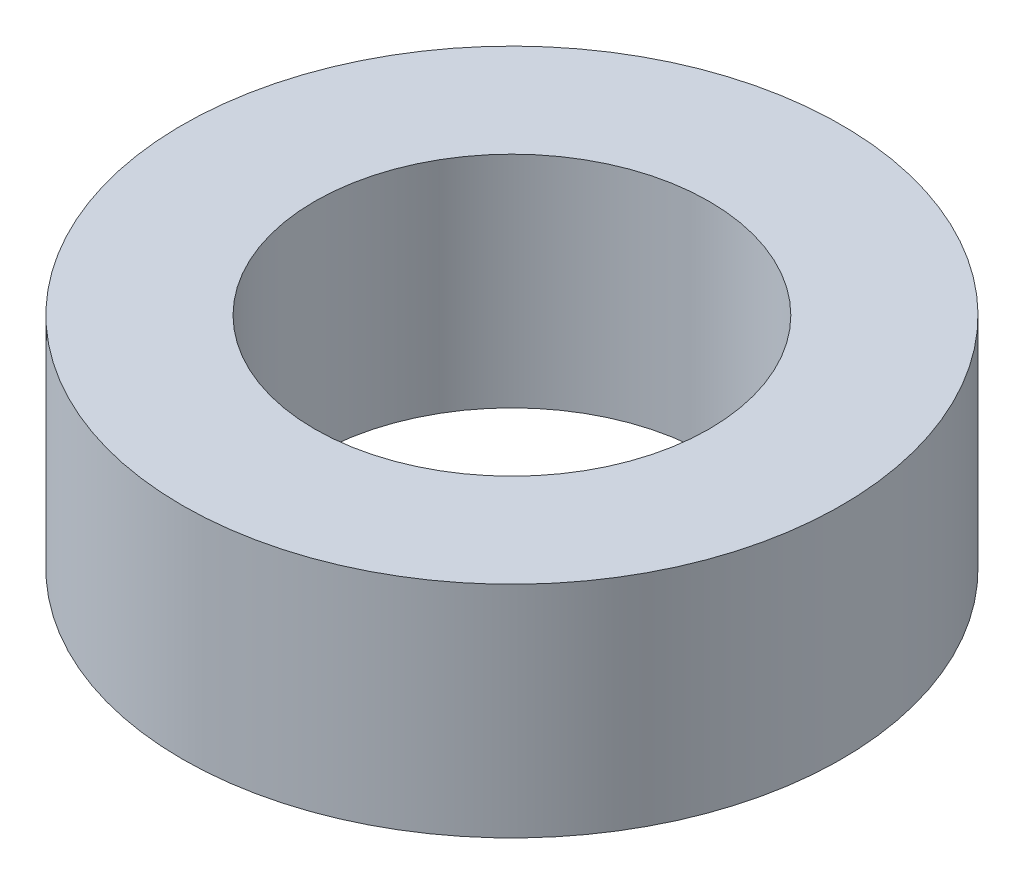
SolidWorks part; units mm, degrees
ref_plane "Front Plane" through (0, 0, 0) normal (0, 0, 1) x (1, 0, 0)
ref_plane "Top Plane" through (0, 0, 0) normal (0, 1, 0) x (1, 0, 0)
ref_plane "Right Plane" through (0, 0, 0) normal (1, 0, 0) x (0, 0, -1)
sketch "Sketch1" plane through (0, 0, 0) normal (0, 1, 0) x (1, 0, 0)
  circle A0 centre (0, 0) radius 4.7625
  circle A1 centre (0, 0) radius 2.85
  dimension "D1" = 9.525
  dimension "D2" = 5.7
extrude "Extrude1" add sketch "Sketch1" along normal blind 3.175
